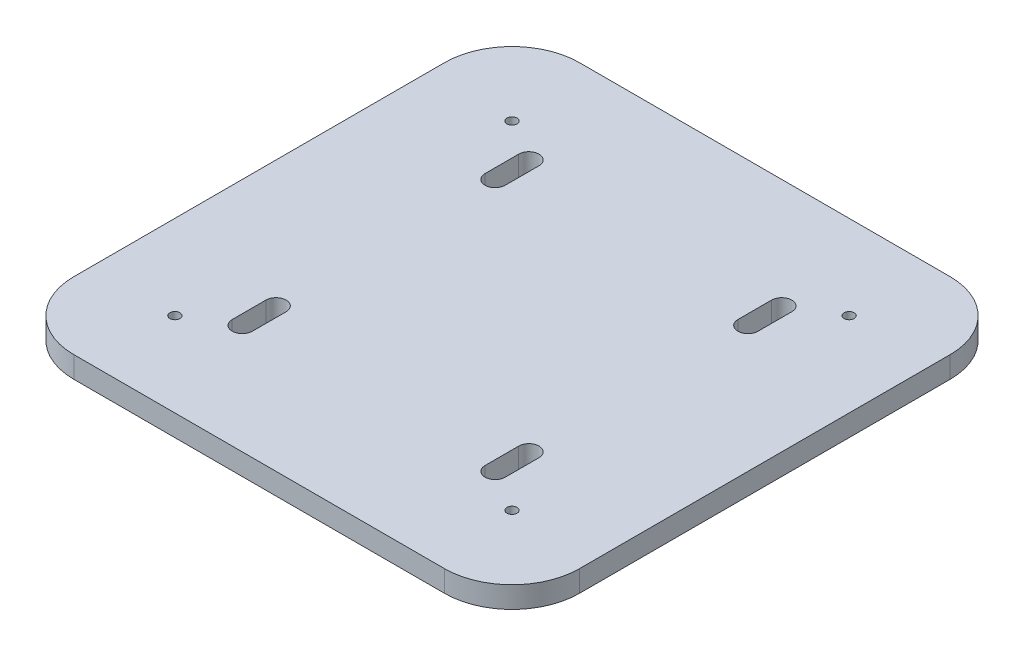
SolidWorks part; units mm, degrees
ref_plane "Front Plane" through (0, 0, 0) normal (0, 0, 1) x (1, 0, 0)
ref_plane "Top Plane" through (0, 0, 0) normal (0, 1, 0) x (1, 0, 0)
ref_plane "Right Plane" through (0, 0, 0) normal (1, 0, 0) x (0, 0, -1)
sketch "Sketch1" plane through (0, 0, 0) normal (0, 1, 0) x (1, 0, 0)
  line L0 (0, 114.196) -> (0, -96.4824) construction
  line L2 (-114.9497, 0) -> (68.2161, 0) construction
  line L4 (-55, 75) -> (55, 75)
  line L5 (75, 55) -> (75, -55)
  line L6 (-55, -75) -> (55, -75)
  line L7 (-75, 55) -> (-75, -55)
  line L8 (55, 55) -> (-55, -55) construction
  arc A0 (75, 55) -> (55, 75) centre (55, 55) ccw
  arc A1 (75, -55) -> (55, -75) centre (55, -55) cw
  arc A2 (-75, -55) -> (-55, -75) centre (-55, -55) ccw
  arc A3 (-75, 55) -> (-55, 75) centre (-55, 55) cw
  circle A4 centre (50, 50) radius 1.5
  circle A5 centre (50, -50) radius 1.5
  circle A6 centre (-50, -50) radius 1.5
  circle A7 centre (-50, 50) radius 1.5
  point P10 (75, 75)
  point P12 (75, 0)
  point P16 (0, -75)
  point P21 (0, 75)
  point P34 (0, 0)
  dimension "D3" = 20
  dimension "D4" = 50
  dimension "D1" = 75
  dimension "D2" = 75
  dimension "D5" = 4
extrude "Boss-Extrude1" add sketch "Sketch1" along normal blind 6.35
sketch "Sketch2" plane through (0, 6.35, 0) normal (0, 1, 0) x (1, 0, 0)
  line L0 (0, 79.0587) -> (0, -54.7909) construction
  line L1 (40.5, 42.5) -> (40.5, 32.5)
  line L2 (-72.9103, 0) -> (51.9385, 0) construction
  line L3 (34.5, 42.5) -> (34.5, 32.5)
  line L4 (-34.5, 42.5) -> (-34.5, 32.5)
  line L5 (-40.5, 42.5) -> (-40.5, 32.5)
  line L6 (40.5, -42.5) -> (40.5, -32.5)
  line L7 (34.5, -42.5) -> (34.5, -32.5)
  line L8 (-34.5, -42.5) -> (-34.5, -32.5)
  line L9 (-40.5, -42.5) -> (-40.5, -32.5)
  arc A0 (-34.5, 42.5) -> (-40.5, 42.5) centre (-37.5, 42.5) ccw
  arc A1 (-40.5, 32.5) -> (-34.5, 32.5) centre (-37.5, 32.5) ccw
  arc A2 (34.5, 42.5) -> (40.5, 42.5) centre (37.5, 42.5) cw
  arc A3 (40.5, 32.5) -> (34.5, 32.5) centre (37.5, 32.5) cw
  arc A4 (40.5, -32.5) -> (34.5, -32.5) centre (37.5, -32.5) ccw
  arc A5 (34.5, -42.5) -> (40.5, -42.5) centre (37.5, -42.5) ccw
  arc A6 (-34.5, -42.5) -> (-40.5, -42.5) centre (-37.5, -42.5) cw
  arc A7 (-40.5, -32.5) -> (-34.5, -32.5) centre (-37.5, -32.5) cw
  point P2 (0, 0)
  point P7 (0, 0)
  dimension "D1" = 10
  dimension "D2" = 3
  dimension "D3" = 37.5
  dimension "D4" = 42.5
extrude "Cut-Extrude1" cut sketch "Sketch2" against normal blind 10
